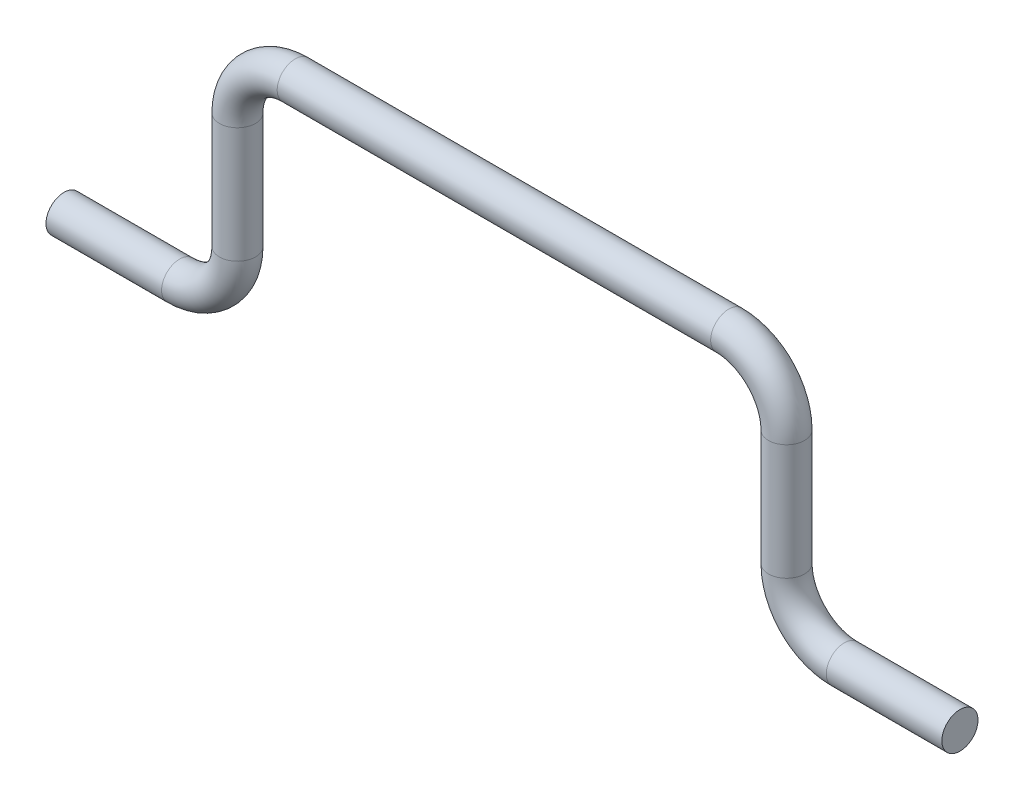
SolidWorks part; units mm, degrees
ref_plane "Front Plane" through (0, 0, 0) normal (0, 0, 1) x (1, 0, 0)
ref_plane "Top Plane" through (0, 0, 0) normal (0, 1, 0) x (1, 0, 0)
ref_plane "Right Plane" through (0, 0, 0) normal (1, 0, 0) x (0, 0, -1)
sketch "Sketch3" plane through (0, 0, 0) normal (1, 0, 0) x (0, 0, -1)
  circle A0 centre (0, 0) radius 3.9688
  dimension "D1" = 7.9375
sketch "Sketch4" plane through (0, 0, 0) normal (0, 0, 1) x (1, 0, 0)
  line L0 (0, 0) -> (25.4, 0)
  line L1 (0, -3.9688) -> (0, 3.9688) construction
  line L2 (38.1, 12.7) -> (38.1, 38.1)
  line L3 (50.8, 50.8) -> (146.05, 50.8)
  line L4 (98.425, 50.8) -> (98.425, 21.1461) construction
  line L5 (158.75, 12.7) -> (158.75, 38.1)
  line L6 (196.85, 0) -> (171.45, 0)
  arc A0 (38.1, 12.7) -> (25.4, 0) centre (25.4, 12.7) cw
  arc A1 (158.75, 38.1) -> (146.05, 50.8) centre (146.05, 38.1) ccw
  arc A2 (50.8, 50.8) -> (38.1, 38.1) centre (50.8, 38.1) ccw
  arc A3 (171.45, 0) -> (158.75, 12.7) centre (171.45, 12.7) cw
  point P13 (38.1, 0)
  point P15 (158.75, 50.8)
  point P18 (38.1, 50.8)
  point P21 (158.75, 0)
  dimension "D4" = 12.7
  dimension "D5" = 12.7
  dimension "D6" = 12.7
  dimension "D1" = 38.1
  dimension "D2" = 50.8
  dimension "D3" = 120.65
sweep "Sweep1" add profiles "Sketch3" path "Sketch4"
